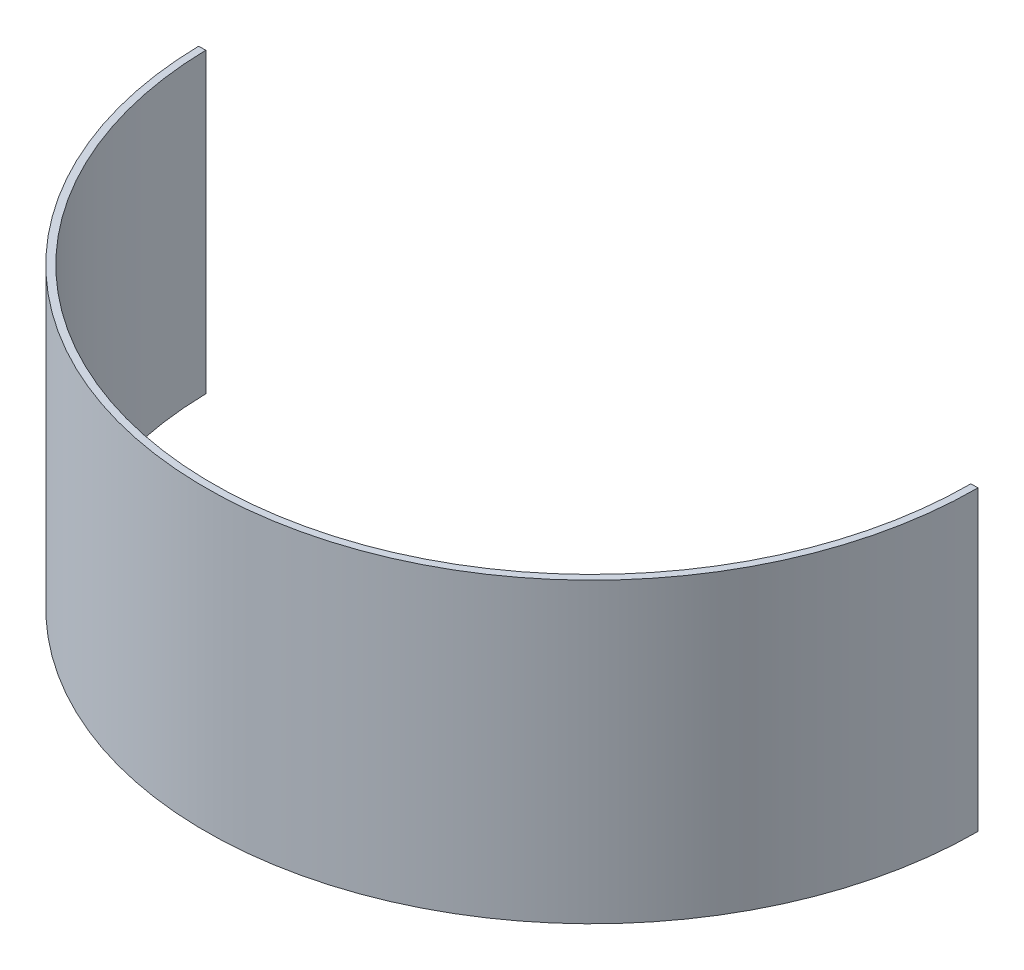
SolidWorks part; units mm, degrees
material "Polycarbonate"
ref_plane "Front Plane" through (0, 0, 0) normal (0, 0, 1) x (1, 0, 0)
ref_plane "Top Plane" through (0, 0, 0) normal (0, 1, 0) x (1, 0, 0)
ref_plane "Right Plane" through (0, 0, 0) normal (1, 0, 0) x (0, 0, -1)
sketch "Sketch1" plane through (0, 0, 0) normal (0, 1, 0) x (1, 0, 0)
  line L2 (169.8625, 0) -> (173.0375, 0)
  line L3 (-169.8328, -3.175) -> (-173.0073, -3.2343)
  line L6 (-50.8, 0) -> (-169.8328, 0) construction
  arc A0 (-169.8328, -3.175) -> (169.8625, 0) centre (0, 0) ccw
  arc A1 (173.0375, 0) -> (-173.0073, -3.2343) centre (0, 0) cw
  arc A2 (0, 50.8) -> (-50.8, 0) centre (0, 0) ccw construction
  dimension "D1" = 169.8625
  dimension "D2" = 3.175
  dimension "D5" = 3.175
  dimension "D4" = 50.8
  dimension "D6" = 3.175
extrude "Boss-Extrude1" add sketch "Sketch1" along normal mid plane 133.35 contours L2 A1 L3 A0
